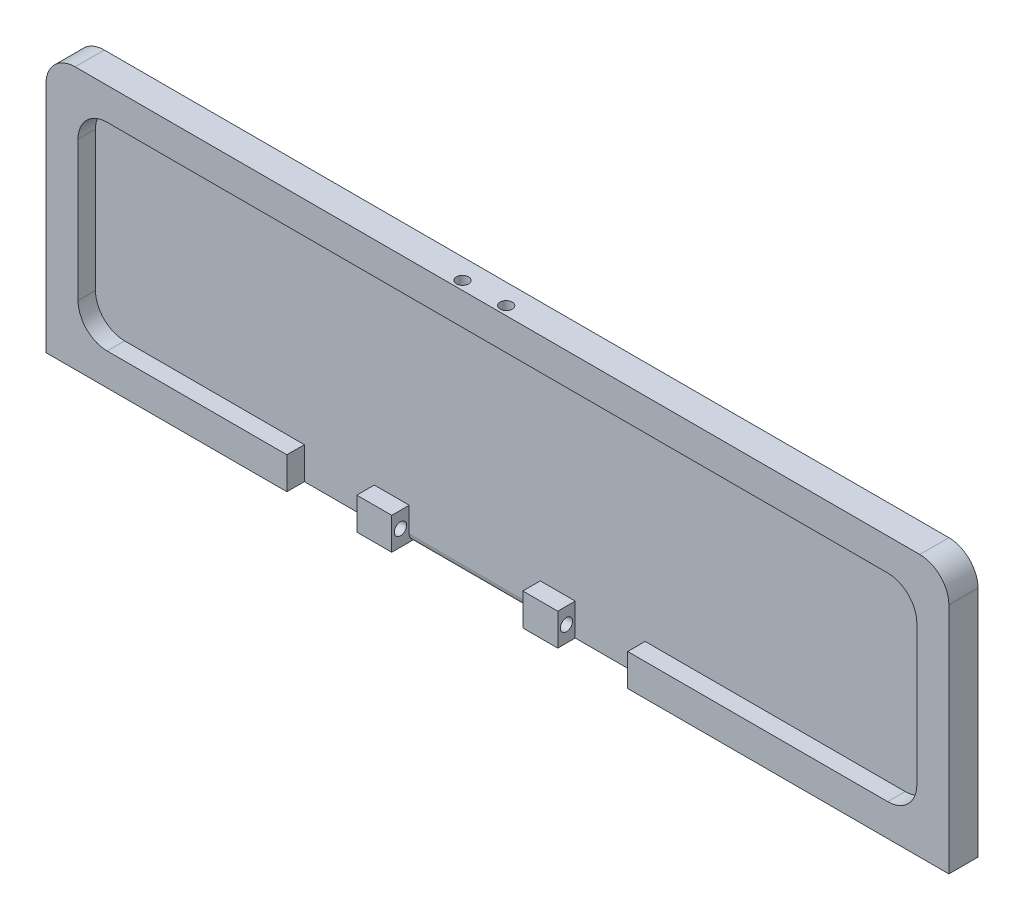
SolidWorks part; units mm, degrees
ref_plane "前视基准面" through (0, 0, 0) normal (0, 0, 1) x (1, 0, 0)
ref_plane "上视基准面" through (0, 0, 0) normal (0, 1, 0) x (1, 0, 0)
ref_plane "右视基准面" through (0, 0, 0) normal (1, 0, 0) x (0, 0, -1)
sketch "草图1" plane through (0, 0, 0) normal (0, 0, 1) x (1, 0, 0)
  line L1 (77.5, -22.5) -> (-77.5, -22.5)
  line L2 (77.5, -22.5) -> (77.5, 22.5)
  line L3 (77.5, 22.5) -> (-77.5, 22.5)
  line L4 (-77.5, -22.5) -> (-77.5, 22.5)
  line L5 (77.5, -22.5) -> (-77.5, 22.5) construction
  line L6 (77.5, 22.5) -> (-77.5, -22.5) construction
  point P0 (0, 0)
  dimension "D1" = 155
  dimension "D2" = 45
extrude "凸台-拉伸1" add sketch "草图1" along normal blind 5
sketch "草图2" plane through (0, 0, 5) normal (0, 0, 1) x (1, 0, 0)
  line L0 (77.5, 22.5) -> (-77.5, 22.5) construction
  line L1 (72, -17) -> (-72, -17)
  line L2 (72, -17) -> (72, 17)
  line L3 (72, 17) -> (-72, 17)
  line L4 (-72, -17) -> (-72, 17)
  line L5 (72, -17) -> (-72, 17) construction
  line L6 (72, 17) -> (-72, -17) construction
  line L7 (-77.5, 22.5) -> (-77.5, -22.5) construction
  point P0 (0, 0)
  dimension "D1" = 5.5
  dimension "D2" = 5.5
extrude "切除-拉伸1" cut sketch "草图2" against normal blind 3
fillet "圆角1" radius 5 2 edges at (77.5, 22.5, 2.5) (-77.5, 22.5, 2.5)
fillet "圆角2" radius 5 4 edges at (-72, 17, 3.5) (-72, -17, 3.5) (72, -17, 3.5) (72, 17, 3.5)
sketch "草图7" plane through (0, 0, 5) normal (0, 0, 1) x (1, 0, 0)
  line L0 (4.3543, -17) -> (4.3543, -22.5)
  line L1 (-67, -17) -> (67, -17) construction
  line L2 (-77.5, -22.5) -> (77.5, -22.5) construction
  line L3 (4.3543, -22.5) -> (-18.1457, -22.5)
  line L4 (-18.1457, -22.5) -> (-18.1457, -17)
  line L5 (-18.1457, -17) -> (4.3543, -17)
  line L9 (3.8543, 5.15) -> (3.8543, -23.5) construction
  line L10 (-17.6457, -23.5) -> (-17.6457, 5.15) construction
  dimension "D1" = 0.5
  dimension "D2" = 0.5
extrude "切除-拉伸2" cut sketch "草图7" against normal blind 3
fillet "圆角7" radius 1.2 1 edges at (-6.8957, -22.5, 2)
sketch "草图9" plane through (0, 0, 5) normal (0, 0, 1) x (1, 0, 0)
  line L0 (10.3543, -22.5) -> (10.3543, -17)
  line L1 (4.3543, -22.5) -> (77.5, -22.5) construction
  line L2 (4.3543, -17) -> (67, -17) construction
  line L3 (10.3543, -17) -> (22.3543, -17)
  line L4 (22.3543, -17) -> (22.3543, -22.5)
  line L5 (22.3543, -22.5) -> (10.3543, -22.5)
  line L6 (4.3543, -22.5) -> (4.3543, -17) construction
  dimension "D1" = 6
  dimension "D2" = 12
extrude "切除-拉伸3" cut sketch "草图9" against normal blind 3
hole_wizard "Ø2.1 (2.1) 直径孔1" positions "草图12" profile "草图11" hole size "Ø2.1" standard "GB"
sketch "草图12" plane through (10.3543, 0, 0) normal (1, 0, 0) x (0, 0, -1)
  line L0 (-5, -22.5) -> (-2, -17) construction
  line L2 (-2, -22.5) -> (-5, -17) construction
  point P0 (-3.5, -19.75)
sketch "草图11" plane through (10.3543, -19.75, 3.5) normal (0, 1, 0) x (0, 0, -1)
  line L0 (0, 0) -> (0, 36.6309)
  line L1 (0, 36.6309) -> (1.05, 36)
  line L2 (1.05, 36) -> (1.05, 0)
  line L5 (1.05, 0) -> (0, 0)
  line L10 (0, 36.6309) -> (-1.05, 36) construction
  line L11 (0, -6.35) -> (0, 107.95) construction
  dimension "孔直径" = 2.1
  dimension "孔深度" = 36
  dimension "导头角度" = 118
hole_wizard "Ø2.1 (2.1) 直径孔2" positions "草图13" profile "草图14" hole size "Ø2.1" standard "GB"
sketch "草图13" plane through (0, 22.5, 0) normal (0, 1, 0) x (1, 0, 0)
  line L0 (72.5, -5) -> (-72.5, -5) construction
  point P0 (0, -3.5)
  point P2 (-7.5, -3.5)
  dimension "D1" = 7.5
  dimension "D2" = 0
  dimension "D3" = 1.5
sketch "草图14" plane through (0, 22.5, 3.5) normal (1, 0, 0) x (0, 0, 1)
  line L0 (0, 0) -> (0, 13.8309)
  line L1 (0, 13.8309) -> (1.05, 13.2)
  line L2 (1.05, 13.2) -> (1.05, 0)
  line L5 (1.05, 0) -> (0, 0)
  line L10 (0, 13.8309) -> (-1.05, 13.2) construction
  line L11 (0, -6.35) -> (0, 107.95) construction
  dimension "孔直径" = 2.1
  dimension "孔深度" = 13.2
  dimension "导头角度" = 118
sketch "草图15" plane through (0, 0, 5) normal (0, 0, 1) x (1, 0, 0)
  line L0 (-24.1457, -22.5) -> (-24.1457, -17)
  line L1 (-77.5, -22.5) -> (-18.1457, -22.5) construction
  line L2 (-67, -17) -> (-18.1457, -17) construction
  line L3 (-24.1457, -17) -> (-36.1457, -17)
  line L4 (-36.1457, -17) -> (-36.1457, -22.5)
  line L5 (-36.1457, -22.5) -> (-24.1457, -22.5)
  line L6 (-18.1457, -17) -> (-18.1457, -22.5) construction
  dimension "D1" = 6
  dimension "D2" = 12
extrude "切除-拉伸4" cut sketch "草图15" against normal up to surface (3 mm away) up to face at (2.3646, -9.725, 2)
